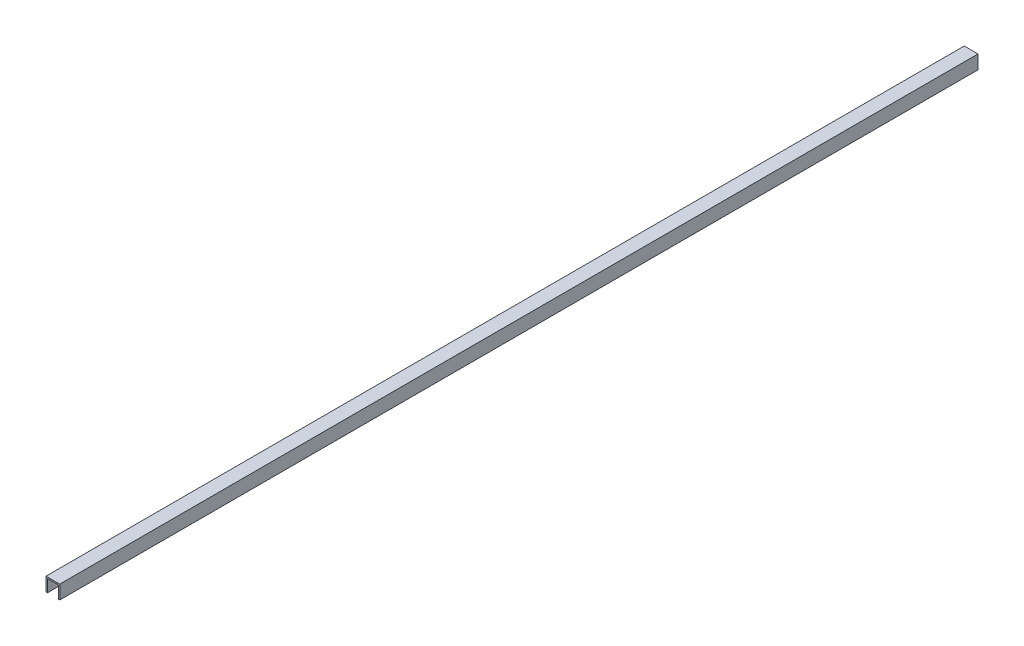
SolidWorks part; units mm, degrees
ref_plane "Спереди" through (0, 0, 0) normal (0, 0, 1) x (1, 0, 0)
ref_plane "Сверху" through (0, 0, 0) normal (0, 1, 0) x (1, 0, 0)
ref_plane "Справа" through (0, 0, 0) normal (1, 0, 0) x (0, 0, -1)
other "Configuration Table"
sketch "Sketch2" plane through (0, 0, 0) normal (0, 0, 1) x (1, 0, 0)
  line L0 (-6, -7.5) -> (-6, 6)
  line L1 (7.5, -7.5) -> (6, -7.5)
  line L2 (7.5, -7.5) -> (7.5, 7.5)
  line L3 (7.5, 7.5) -> (-7.5, 7.5)
  line L4 (-7.5, -7.5) -> (-7.5, 7.5)
  line L5 (7.5, -7.5) -> (-7.5, 7.5) construction
  line L6 (7.5, 7.5) -> (-7.5, -7.5) construction
  line L7 (-6, 6) -> (6, 6)
  line L8 (6, 6) -> (6, -7.5)
  line L9 (0, 7.5) -> (0, -12.4687) construction
  line L10 (-6, -7.5) -> (-7.5, -7.5)
  point P0 (0, 0)
  dimension "D1" = 15
  dimension "D2" = 15
  dimension "D3" = 1.5
  dimension "D4" = 1.5
extrude "Boss-Extrude1" add sketch "Sketch2" along normal mid plane 1000
sketch "Sketch3" plane through (0, 6, 0) normal (0, -1, 0) x (1, 0, 0)
  line L0 (0, 500) -> (0, -500) construction
  line L1 (-6, 500) -> (6, 500) construction
  line L2 (-6, -500) -> (6, -500) construction
  line L3 (-6, 0) -> (6, 0) construction
  line L4 (-6, 500) -> (-6, -500) construction
  line L5 (6, 500) -> (6, -500) construction
